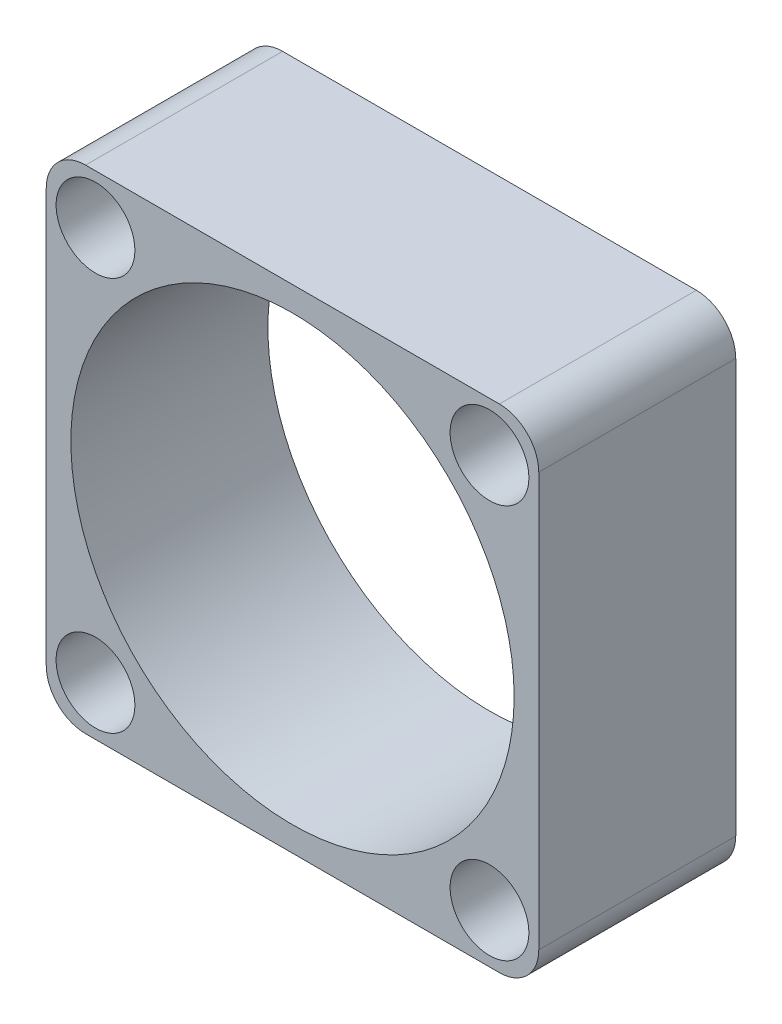
SolidWorks part; units mm, degrees
material "ABS PC"
ref_plane "Front Plane" through (0, 0, 0) normal (0, 0, 1) x (1, 0, 0)
ref_plane "Top Plane" through (0, 0, 0) normal (0, 1, 0) x (1, 0, 0)
ref_plane "Right Plane" through (0, 0, 0) normal (1, 0, 0) x (0, 0, -1)
sketch "Sketch1" plane through (0, 0, 0) normal (0, 0, 1) x (1, 0, 0)
  line L1 (0, 0) -> (25, 0)
  line L2 (0, 0) -> (0, 25)
  line L3 (0, 25) -> (25, 25)
  line L4 (25, 0) -> (25, 25)
  dimension "D1" = 25
  dimension "D2" = 25
extrude "Boss-Extrude1" add sketch "Sketch1" along normal blind 10
sketch "Sketch3" plane through (0, 0, 10) normal (0, 0, 1) x (1, 0, 0)
  line L0 (0, 12.5) -> (12.5, 12.5) construction
  line L1 (0, 25) -> (0, 0) construction
  line L2 (12.5, 12.5) -> (12.5, 0) construction
  line L3 (0, 0) -> (25, 0) construction
  circle A0 centre (12.5, 12.5) radius 11.25
  circle A1 centre (2.5, 22.5) radius 2
  circle A2 centre (22.5, 22.5) radius 2
  circle A3 centre (22.5, 2.5) radius 2
  circle A4 centre (2.5, 2.5) radius 2
  dimension "D1" = 22.5
  dimension "D6" = 4
  dimension "D2" = 20
  dimension "D3" = 20
  dimension "D4" = 20
  dimension "D5" = 20
extrude "Cut-Extrude1" cut sketch "Sketch3" against normal blind 10 contours A0 | A1 | A4 | A3 | A2
fillet "Fillet1" radius 2 4 edges at (0, 0, 5) (25, 0, 5) (0, 25, 5) (25, 25, 5)
